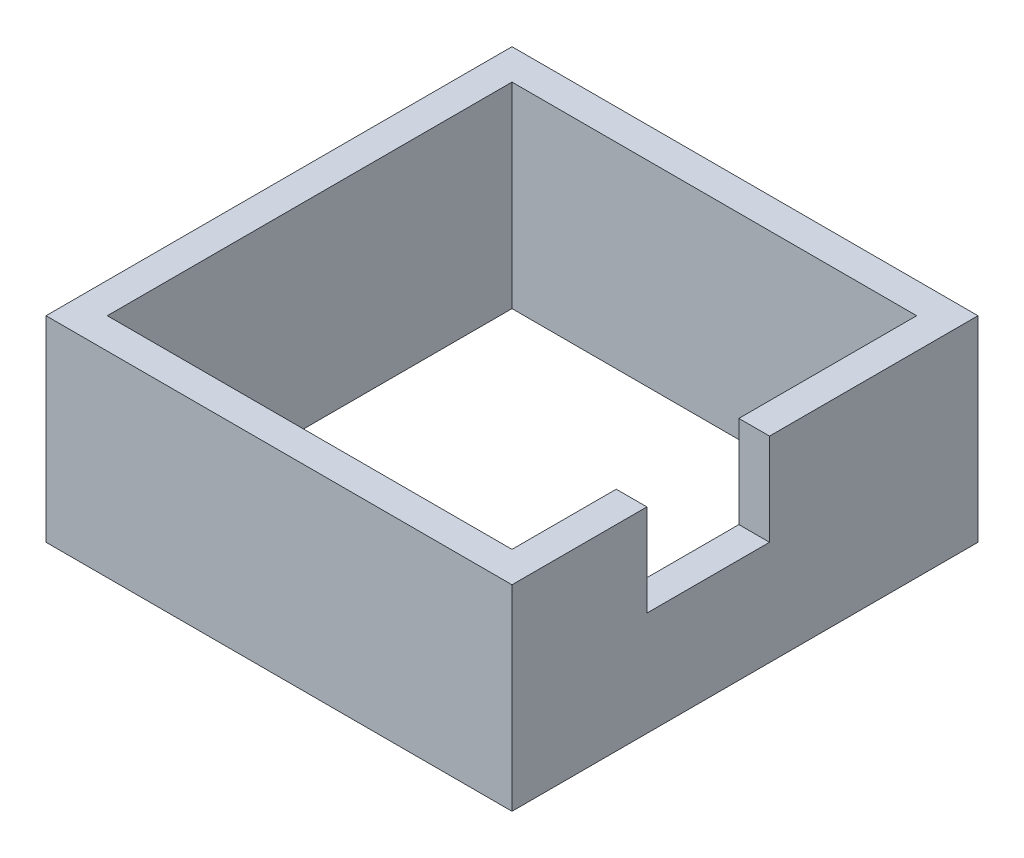
SolidWorks part; units mm, degrees
ref_plane "Front Plane" through (0, 0, 0) normal (0, 0, 1) x (1, 0, 0)
ref_plane "Top Plane" through (0, 0, 0) normal (0, 1, 0) x (1, 0, 0)
ref_plane "Right Plane" through (0, 0, 0) normal (1, 0, 0) x (0, 0, -1)
sketch "Sketch1" plane through (0, 0, 0) normal (0, 1, 0) x (1, 0, 0)
  line L1 (-19, 19) -> (19, 19)
  line L2 (-19, 19) -> (-19, -19)
  line L3 (-19, -19) -> (19, -19)
  line L4 (19, 19) -> (19, -19)
  line L5 (-16.5, 16.5) -> (16.5, 16.5)
  line L6 (-16.5, 16.5) -> (-16.5, -16.5)
  line L7 (-16.5, -16.5) -> (16.5, -16.5)
  line L8 (16.5, 16.5) -> (16.5, -16.5)
  point P4 (0, 19)
  point P6 (-19, 0)
  point P11 (0, -16.5)
  point P12 (16.5, 0)
  dimension "D1" = 38
  dimension "D2" = 38
  dimension "D3" = 2.5
  dimension "D4" = 2.5
extrude "Boss-Extrude1" add sketch "Sketch1" along normal blind 16
sketch "Sketch2" plane through (19, 0, 0) normal (1, 0, 0) x (0, 0, -1)
  line L0 (-19, 16) -> (19, 16) construction
  line L1 (-8, 16) -> (2, 16)
  line L2 (-8, 16) -> (-8, 8.5)
  line L3 (-8, 8.5) -> (2, 8.5)
  line L4 (2, 16) -> (2, 8.5)
  line L5 (-19, 16) -> (-19, 0) construction
  dimension "D1" = 11
  dimension "D2" = 7.5
  dimension "D3" = 10
extrude "Cut-Extrude1" cut sketch "Sketch2" against normal up to surface (2.5 mm away) up to face at (16.5, 8, 0)
